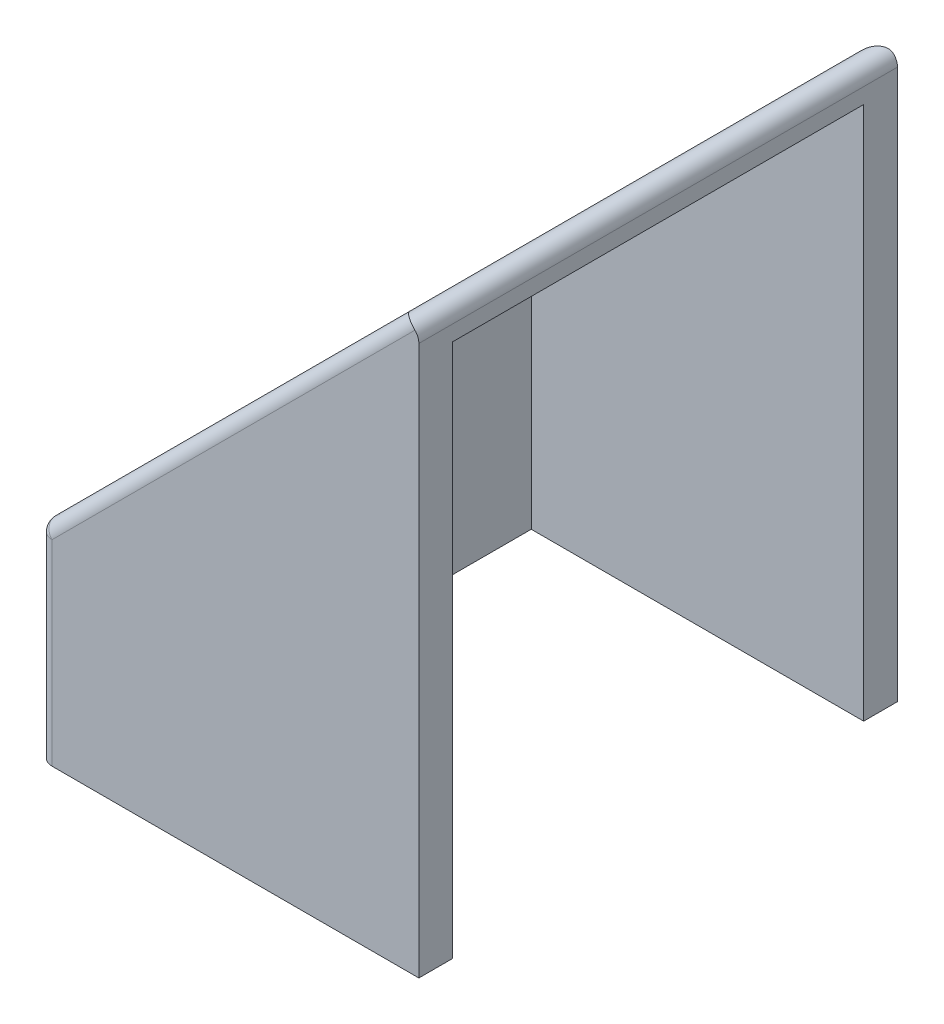
SolidWorks part; units mm, degrees
ref_plane "Front Plane" through (0, 0, 0) normal (0, 0, 1) x (1, 0, 0)
ref_plane "Top Plane" through (0, 0, 0) normal (0, 1, 0) x (1, 0, 0)
ref_plane "Right Plane" through (0, 0, 0) normal (1, 0, 0) x (0, 0, -1)
sketch "Sketch1" plane through (0, 0, 0) normal (0, 0, 1) x (1, 0, 0)
  line L0 (0, 0) -> (17.9605, 17.9605)
  line L1 (17.9605, 17.9605) -> (17.9605, 0)
  line L2 (17.9605, 0) -> (0, 0)
  dimension "D1" = 25.4
  dimension "D2" = 45
extrude "Boss-Extrude1" add sketch "Sketch1" along normal blind 22.606
sketch "Sketch2" plane through (17.9605, 0, 0) normal (1, 0, 0) x (0, 0, -1)
  line L7 (-21.006, 0) -> (-1.6, 0)
  line L10 (-1.6, 0) -> (-1.6, 16.3605)
  line L11 (-21.006, 16.3605) -> (-21.006, 0)
  line L12 (-1.6, 16.3605) -> (-21.006, 16.3605)
  line L13 (-1.6, 0) -> (-1.6, 16.3605)
  line L14 (-21.006, 16.3605) -> (-21.006, 0)
  line L15 (-1.6, 16.3605) -> (-21.006, 16.3605)
  dimension "D1" = 1.6
extrude "Cut-Extrude1" cut sketch "Sketch2" against normal offset from surface (15.6978 mm away) 1.6
sketch "Sketch3" plane through (0, 0, 0) normal (0, -1, 0) x (1, 0, 0)
  line L0 (17.9605, 22.606) -> (0, 22.606)
  line L1 (0, 22.606) -> (0, 0)
  line L2 (0, 0) -> (17.9605, 0)
  line L3 (17.9605, 0) -> (17.9605, 1.6)
  line L4 (17.9605, 1.6) -> (2.2627, 1.6)
  line L5 (2.2627, 1.6) -> (2.2627, 21.006)
  line L6 (2.2627, 21.006) -> (17.9605, 21.006)
  line L7 (17.9605, 21.006) -> (17.9605, 22.606)
extrude "Boss-Extrude2" add sketch "Sketch3" along normal blind 9.525
fillet "Fillet1" radius 0.635 6 edges at (17.9605, 17.9605, 11.303) (0, 0, 11.303) (8.9803, 8.9803, 0) (8.9803, 8.9803, 22.606) (0, -4.7625, 0) (0, -4.7625, 22.606)
